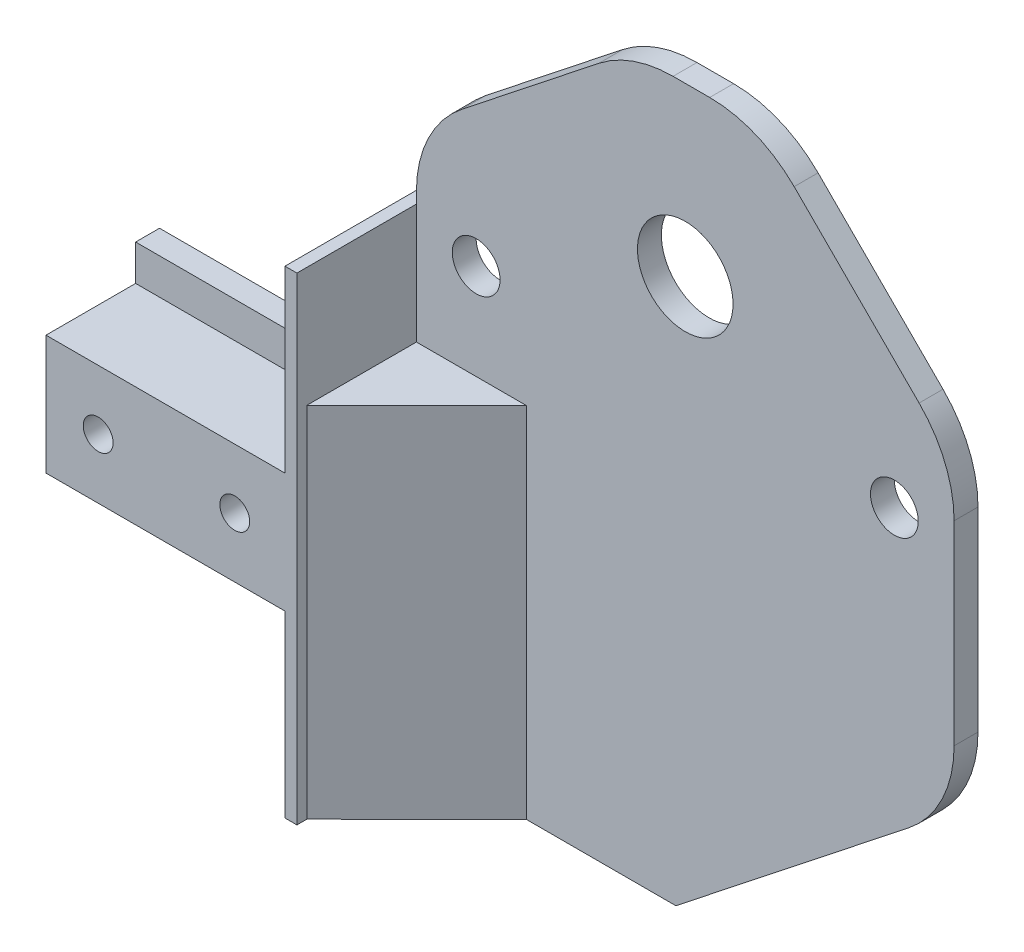
SolidWorks part; units mm, degrees
ref_plane "Front Plane" through (0, 0, 0) normal (0, 0, 1) x (1, 0, 0)
ref_plane "Top Plane" through (0, 0, 0) normal (0, 1, 0) x (1, 0, 0)
ref_plane "Right Plane" through (0, 0, 0) normal (1, 0, 0) x (0, 0, -1)
sketch "Sketch2" plane through (0, 0, 0) normal (0, 0, 1) x (1, 0, 0)
  line L1 (10, -5) -> (-10, -5)
  line L2 (10, -5) -> (10, 5)
  line L3 (10, 5) -> (-10, 5)
  line L4 (-10, -5) -> (-10, 5)
  line L5 (0, 5) -> (0, -5) construction
  line L6 (10, 0) -> (-10, 0) construction
  point P0 (0, 0)
  dimension "D1" = 20
  dimension "D2" = 10
extrude "Boss-Extrude1" add sketch "Sketch2" along normal blind 11
sketch "Sketch3" plane through (0, 5, 0) normal (0, 1, 0) x (1, 0, 0)
  line L1 (-10, -3.5) -> (10, -3.5)
  line L2 (-10, -3.5) -> (-10, -1.5)
  line L3 (-10, -1.5) -> (10, -1.5)
  line L4 (10, -3.5) -> (10, -1.5)
  line L5 (0, -1.5) -> (0, -3.5) construction
  line L6 (-10, -2.5) -> (10, -2.5) construction
  line L7 (10, -11) -> (-10, -11) construction
  point P0 (0, -2.5)
  dimension "D1" = 20
  dimension "D2" = 7.5
  dimension "D3" = 2
extrude "Boss-Extrude2" add sketch "Sketch3" along normal blind 3 and the other way blind 13
sketch "Sketch4" plane through (10, 0, 0) normal (1, 0, 0) x (0, 0, -1)
  line L0 (-11, -5) -> (-11, 5) construction
  line L1 (1, 20) -> (-11, 20)
  line L2 (1, 20) -> (1, -20)
  line L3 (1, -20) -> (-11, -20)
  line L4 (-11, 20) -> (-11, -20)
  line L5 (-5, -20) -> (-5, 20) construction
  line L6 (1, 0) -> (-11, 0) construction
  line L8 (-11, -5) -> (-3.5, -5) construction
  line L10 (-11, 5) -> (-3.5, 5) construction
  point P0 (-5, 0)
  point P6 (0, 0)
  dimension "D1" = 40
  dimension "D2" = 12
  dimension "D3" = 0
  dimension "D4" = 15
  dimension "D5" = 15
extrude "Boss-Extrude3" add sketch "Sketch4" along normal blind 1
sketch "Sketch5" plane through (11, 0, 0) normal (1, 0, 0) x (0, 0, -1)
  line L1 (-11, -20) -> (1, -20) construction
  line L2 (1, -20) -> (-1, -20)
  line L3 (1, -20) -> (1, 40)
  line L4 (1, 40) -> (-1, 40)
  line L5 (-1, -20) -> (-1, 40)
  line L6 (0, 40) -> (0, -20) construction
  line L9 (1, 10) -> (-1, 10) construction
  line L10 (-11, 20) -> (-11, -20) construction
  point P0 (0, 10)
  dimension "D1" = 0
  dimension "D2" = 60
  dimension "D3" = 2
  dimension "D4" = 10
extrude "Boss-Extrude4" add sketch "Sketch5" along normal blind 45
hole_wizard "Ø4.0mm Dowel Slot1" positions "Sketch12" profile "Sketch13" size "Ø4.0" standard "ANSI Metric" slot yes end condition through all
sketch "Sketch12" plane through (0, 0, 1) normal (0, 0, 1) x (1, 0, 0)
  line L0 (11, 40) -> (11, 20) construction
  line L2 (56, 40) -> (11, 40) construction
  point P0 (16, 18)
  point P2 (51, 18)
  dimension "D1" = 5
  dimension "D2" = 35
  dimension "D3" = 22
sketch "Sketch13" plane through (16, 18, 1) normal (1, 0, 0) x (0, -1, 0)
  line L0 (0, 0) -> (0, 2)
  line L1 (0, 2) -> (2, 2)
  line L2 (2, 2) -> (2, 0)
  line L5 (2, 0) -> (0, 0)
  line L11 (0, -6.35) -> (0, 107.95) construction
  dimension "Thru Hole Dia." = 4
  dimension "Thru Hole Depth" = 2
hole_wizard "Ø8.0mm Dowel Slot4" positions "Sketch16" profile "Sketch17" size "Ø8.0" standard "ANSI Metric" slot yes end condition through all
sketch "Sketch16" plane through (0, 0, 1) normal (0, 0, 1) x (1, 0, 0)
  line L0 (56, 40) -> (11, 40) construction
  line L2 (56, 40) -> (56, -20) construction
  point P0 (33.5, 26)
  point P7 (11, 26.1064)
  dimension "D1" = 14
  dimension "D2" = 22.5
sketch "Sketch17" plane through (33.5, 26, 1) normal (1, 0, 0) x (0, -1, 0)
  line L0 (0, 0) -> (0, 2)
  line L1 (0, 2) -> (4, 2)
  line L2 (4, 2) -> (4, 0)
  line L5 (4, 0) -> (0, 0)
  line L11 (0, -6.35) -> (0, 107.95) construction
  dimension "Thru Hole Dia." = 8
  dimension "Thru Hole Depth" = 2
ref_plane "Plane1" through (11, 20, 1) normal (0, -1, 0) x (-1, 0, 0)
ref_plane "Plane2" through (11, -20, 1) normal (0, -1, 0) x (-1, 0, 0)
sketch "Sketch22" plane through (11, -20, 1) normal (0, -1, 0) x (-1, 0, 0)
  line L0 (0, -10) -> (0, 0) construction
  line L1 (0, -9.1673) -> (-9.2025, -9.1673)
  line L2 (0, -9.1673) -> (0, 0)
  line L3 (0, 0) -> (-9.2025, 0)
  line L4 (-9.2025, -9.1673) -> (-9.2025, 0)
  line L5 (-4.6012, 0) -> (-4.6012, -9.1673) construction
  line L6 (0, -4.5837) -> (-9.2025, -4.5837) construction
  line L7 (-45, 0) -> (0, 0) construction
  point P0 (-4.6012, -4.5837)
  dimension "D1" = 0
  dimension "D2" = 0
extrude "Boss-Extrude5" add sketch "Sketch22" along normal blind 0.001 and the other way blind 30
sketch "Sketch23" plane through (0, 10, 0) normal (0, 1, 0) x (1, 0, 0)
  line L0 (20.2025, -1) -> (11, -10.1673)
  line L1 (20.2025, -10.1673) -> (11, -10.1673) construction
  line L2 (11, -10.1673) -> (11, -1) construction
  line L3 (11, -10.1673) -> (20.2025, -10.1673)
  line L4 (20.2025, -10.1673) -> (20.2025, -1)
extrude "Cut-Extrude1" cut sketch "Sketch23" against normal blind 31
hole_wizard "Ø2.5mm Dowel Slot1" positions "Sketch24" profile "Sketch25" size "Ø2.5" standard "ANSI Metric" slot yes end condition through all
sketch "Sketch24" plane through (0, 0, 11) normal (0, 0, 1) x (1, 0, 0)
  point P0 (-5.6335, 0)
  point P2 (5.798, 0)
sketch "Sketch25" plane through (-5.6335, 0, 11) normal (1, 0, 0) x (0, -1, 0)
  line L0 (0, 0) -> (0, 12)
  line L1 (0, 12) -> (1.25, 12)
  line L2 (1.25, 12) -> (1.25, 0)
  line L5 (1.25, 0) -> (0, 0)
  line L11 (0, -6.35) -> (0, 107.95) construction
  dimension "Thru Hole Dia." = 2.5
  dimension "Thru Hole Depth" = 12
sketch "Sketch26" plane through (0, 0, 1) normal (0, 0, 1) x (1, 0, 0)
  line L0 (29.0039, 40) -> (11, 25.7632)
  line L1 (56, 40) -> (11, 40) construction
  line L2 (11, 40) -> (11, 20) construction
  line L3 (11, 25.7632) -> (11, 40)
  line L4 (11, 40) -> (29.0039, 40)
  line L5 (56, 40) -> (39.6868, 40)
  line L6 (39.6868, 40) -> (56, 23.6868)
  line L7 (56, 40) -> (56, -20) construction
  line L8 (56, 23.6868) -> (56, 40)
extrude "Cut-Extrude2" cut sketch "Sketch26" against normal blind 10
sketch "Sketch27" plane through (0, 0, 1) normal (0, 0, 1) x (1, 0, 0)
  line L0 (56, -20) -> (20.2025, -20) construction
  line L1 (32.7139, -20) -> (56, -1.6115)
  line L2 (56, 23.6868) -> (56, -20) construction
  line L3 (56, -1.6115) -> (56, -20)
  line L4 (56, -20) -> (32.7139, -20)
  line L5 (32.7139, -20) -> (32.7544, -19.9926)
extrude "Cut-Extrude3" cut sketch "Sketch27" against normal blind 10 contours L1 L3 L4
fillet "Fillet1" radius 10 5 edges at (56, -1.6115, 0) (56, 23.6868, 0) (39.6868, 40, 0) (29.0039, 40, 0) (11, 25.7632, 0)
